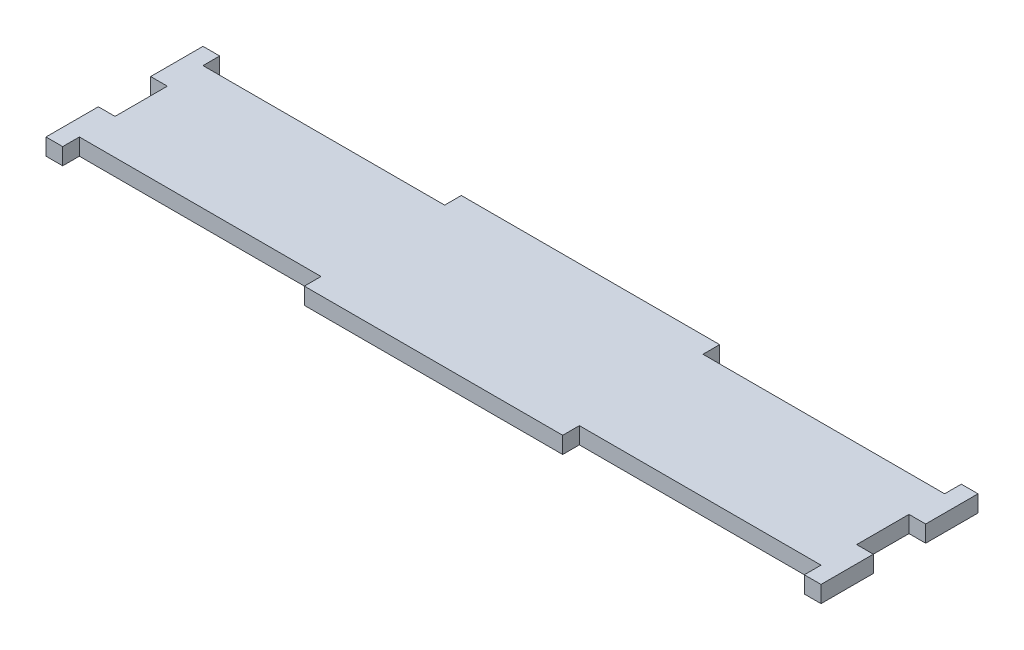
SolidWorks part; units mm, degrees
ref_plane "Front Plane" through (0, 0, 0) normal (0, 0, 1) x (1, 0, 0)
ref_plane "Top Plane" through (0, 0, 0) normal (0, 1, 0) x (1, 0, 0)
ref_plane "Right Plane" through (0, 0, 0) normal (1, 0, 0) x (0, 0, -1)
sketch "Sketch1" plane through (0, 0, 0) normal (0, 1, 0) x (1, 0, 0)
  line L0 (-62.7, 12.7) -> (-60, 12.7)
  line L1 (-60, 10) -> (-20.9, 10)
  line L2 (-60, 4.2333) -> (-60, -4.2333)
  line L3 (-60, -10) -> (-20.9, -10)
  line L4 (60, 4.2333) -> (60, -4.2333)
  line L7 (62.7, 12.7) -> (62.7, 4.2333)
  line L8 (-62.7, -12.7) -> (-60, -12.7)
  line L9 (-62.7, 12.7) -> (-62.7, 4.2333)
  line L10 (-60, 10) -> (-60, 12.7)
  line L11 (-60, -10) -> (-60, -12.7)
  line L12 (60, 10) -> (60, 12.7)
  line L13 (60, -10) -> (60, -12.7)
  line L14 (-20.9, 12.7) -> (20.9, 12.7)
  line L15 (-62.7, 12.7) -> (62.7, 12.7) construction
  line L16 (60, 12.7) -> (62.7, 12.7)
  line L17 (-20.9, -12.7) -> (20.9, -12.7)
  line L18 (-62.7, -12.7) -> (62.7, -12.7) construction
  line L19 (60, -12.7) -> (62.7, -12.7)
  line L20 (-20.9, 12.7) -> (-20.9, 10)
  line L21 (20.9, 12.7) -> (20.9, 10)
  line L22 (20.9, -12.7) -> (20.9, -10)
  line L23 (-20.9, -12.7) -> (-20.9, -10)
  line L25 (-62.7, 12.7) -> (-62.7, -12.7) construction
  line L26 (-62.7, -4.2333) -> (-62.7, -12.7)
  line L28 (62.7, 12.7) -> (62.7, -12.7) construction
  line L29 (62.7, -4.2333) -> (62.7, -12.7)
  line L30 (-62.7, 4.2333) -> (-60, 4.2333)
  line L31 (-62.7, -4.2333) -> (-60, -4.2333)
  line L32 (62.7, 4.2333) -> (60, 4.2333)
  line L33 (62.7, -4.2333) -> (60, -4.2333)
  line L34 (20.9, 10) -> (60, 10)
  line L35 (-60, 10) -> (60, 10) construction
  line L36 (60, 10) -> (60, -10) construction
  line L37 (20.9, -10) -> (60, -10)
  line L38 (-60, -10) -> (60, -10) construction
  line L39 (-60, 10) -> (-60, -10) construction
  point P0 (0, 0)
  point P10 (0, 0)
  point P30 (0, 0)
  point P32 (0, 0)
  point P33 (0, 0)
  point P34 (0, 0)
  point P35 (0, 0)
  point P36 (0, 0)
  point P38 (0, 0)
  point P39 (0, 0)
  point P59 (0, 0)
  point P69 (40, 0)
  dimension "D1" = 20
  dimension "D2" = 120
  dimension "D3" = 2.7
extrude "Boss-Extrude1" add sketch "Sketch1" along normal blind 2.7
